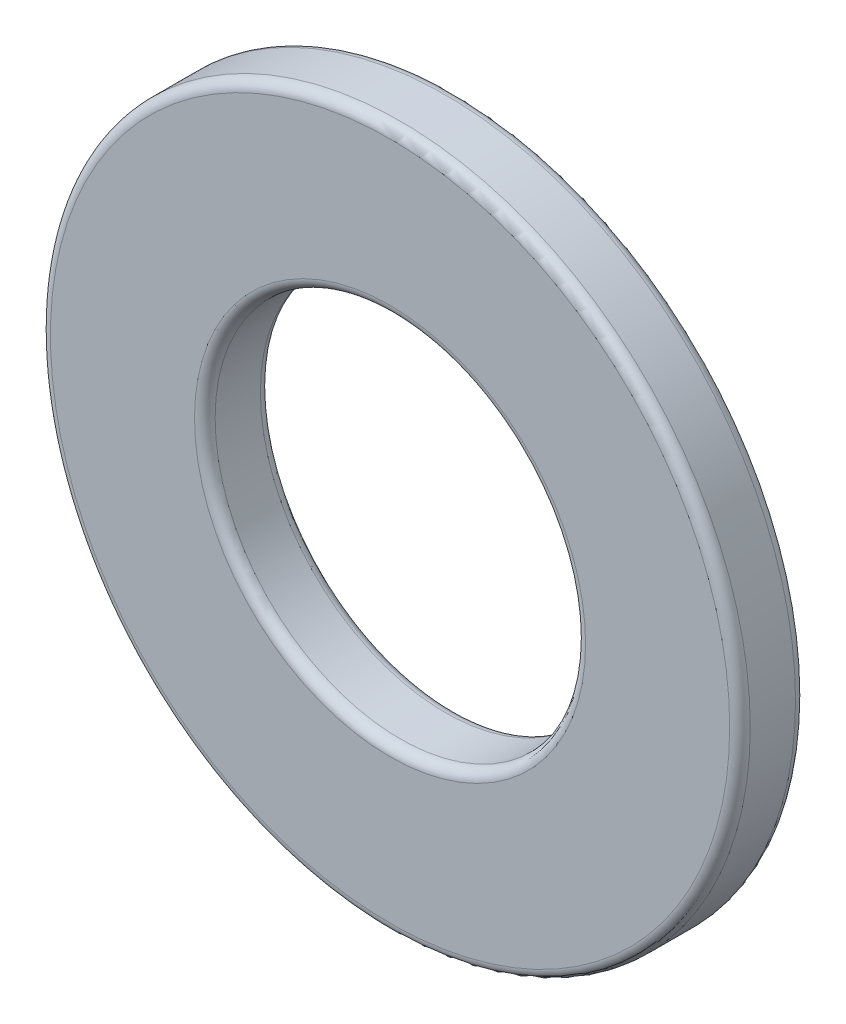
SolidWorks part; units mm, degrees
ref_plane "Front Plane" through (0, 0, 0) normal (0, 0, 1) x (1, 0, 0)
ref_plane "Top Plane" through (0, 0, 0) normal (0, 1, 0) x (1, 0, 0)
ref_plane "Right Plane" through (0, 0, 0) normal (1, 0, 0) x (0, 0, -1)
sketch "Sketch1" plane through (0, 0, 0) normal (0, 0, 1) x (1, 0, 0)
  circle A0 centre (0, 0) radius 4.5
  circle A1 centre (0, 0) radius 8.5
extrude "Boss-Extrude1" add sketch "Sketch1" along normal blind 1.6
fillet "Fillet1" radius 0.25 4 edges at (8.5, 0, 1.6) (4.5, 0, 0) (8.5, 0, 0) (4.5, 0, 1.6)
